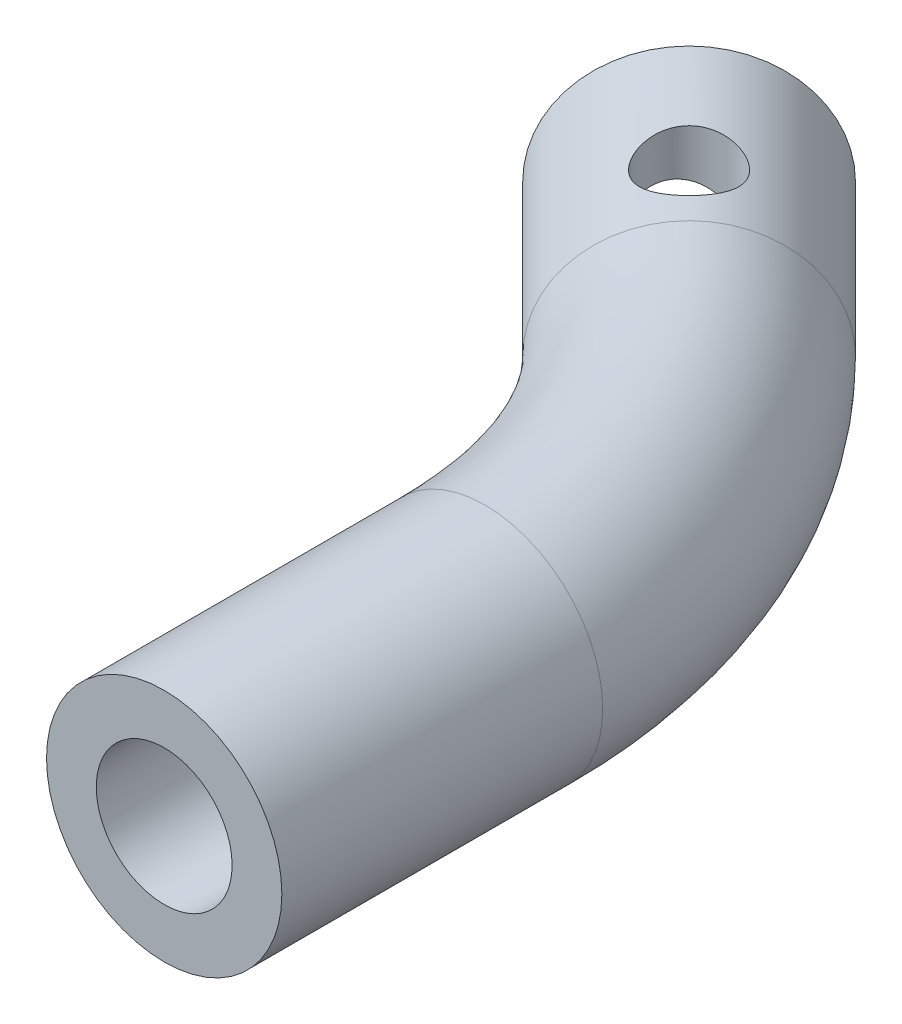
SolidWorks part; units mm, degrees
ref_plane "Front Plane" through (0, 0, 0) normal (0, 0, 1) x (1, 0, 0)
ref_plane "Top Plane" through (0, 0, 0) normal (0, 1, 0) x (1, 0, 0)
ref_plane "Right Plane" through (0, 0, 0) normal (1, 0, 0) x (0, 0, -1)
sketch "PROFILE" plane through (0, 0, 0) normal (0, 1, 0) x (1, 0, 0)
  line L0 (2.5, -10) -> (2.5, -25)
  line L1 (-4.2432, 6.2795) -> (-11.3143, 13.3506)
  line L2 (0, 0) -> (-28.2539, 0) construction
  arc A0 (2.5, -10) -> (-4.2432, 6.2795) centre (-20.5227, -10) ccw
  dimension "D1" = 45
  dimension "D2" = 10
  dimension "D3" = 2.5
  dimension "D4" = 17.5
  dimension "D5" = 15
  dimension "D6" = 25
ref_plane "Plane1" through (0, 0, 25) normal (0, 0, 1) x (1, 0, 0)
sketch "Sketch4" plane through (0, 0, 25) normal (0, 0, 1) x (1, 0, 0)
  circle A0 centre (2.5, 0) radius 5.5
  point P4 (0, 0)
  point P6 (0, 0)
  dimension "D1" = 11
sweep "Sweep2" add profiles "Sketch4" path "PROFILE"
sketch "Sketch6" plane through (0, 0, 25) normal (0, 0, 1) x (1, 0, 0)
  circle A0 centre (2.5, 0) radius 3.175
extrude "HOLE_SHAFT" cut sketch "Sketch6" against normal blind 10
sketch "Sketch7" plane through (-12.3324, 0, -12.3324) normal (-0.7071, 0, -0.7071) x (-0.7071, 0, 0.7071)
  line L0 (5.3033, 0) -> (-1.4399, 0) construction
  circle A0 centre (-0.5744, 0) radius 3.4
  point P3 (0, 0)
  point P4 (-0.5744, 0)
extrude "HOLE_POT" cut sketch "Sketch7" against normal blind 10
sketch "Sketch8" plane through (0, 0, 0) normal (0, 1, 0) x (1, 0, 0)
  line L0 (-4.2432, 6.2795) -> (-11.3143, 13.3506) construction
  circle A0 centre (-6.6736, 8.7099) radius 2
extrude "HOLE_INSERT" cut sketch "Sketch8" along normal through all
sketch "Sketch9" plane through (-5.2613, 0, -5.2613) normal (-0.7071, 0, -0.7071) x (-0.7071, 0, 0.7071)
  line L0 (-2.2229, 2.9736) -> (1.8712, -2.3619) construction
  line L1 (-2.2229, 2.9736) -> (2.4526, -1.5483)
  line L3 (-3.0167, 2.3654) -> (1.8712, -2.3619)
  line L5 (-0.5744, 0) -> (-4.9947, 0) construction
  circle A0 centre (-0.5744, 0) radius 3.4 construction
  arc A1 (-2.2229, 2.9736) -> (-3.0167, 2.3654) centre (-0.5744, 0) ccw
  arc A2 (1.8712, -2.3619) -> (2.4526, -1.5483) centre (-0.5744, 0) ccw
  dimension "D1" = 1
  dimension "D2" = 52.5
extrude "Boss-Extrude2" [suppressed] add sketch "Sketch9" along normal blind 1
sketch "Sketch11" plane through (-5.2613, 0, -5.2613) normal (-0.7071, 0, -0.7071) x (-0.7071, 0, 0.7071)
  line L0 (-0.9055, 3.3838) -> (0.7267, -3.1412)
  line L3 (-1.8756, 3.1412) -> (-0.2434, -3.3838)
  line L4 (-1.8756, 3.1412) -> (0.7267, -3.1412) construction
  line L5 (5.3033, 0) -> (-1.4399, 0) construction
  circle A0 centre (-0.5744, 0) radius 3.4 construction
  arc A1 (-0.2434, -3.3838) -> (0.7267, -3.1412) centre (-0.5744, 0) ccw
  arc A2 (-0.9055, 3.3838) -> (-1.8756, 3.1412) centre (-0.5744, 0) ccw
  dimension "D1" = 1
  dimension "D2" = 67.5
extrude "Boss-Extrude3" add sketch "Sketch11" along normal blind 1.5
